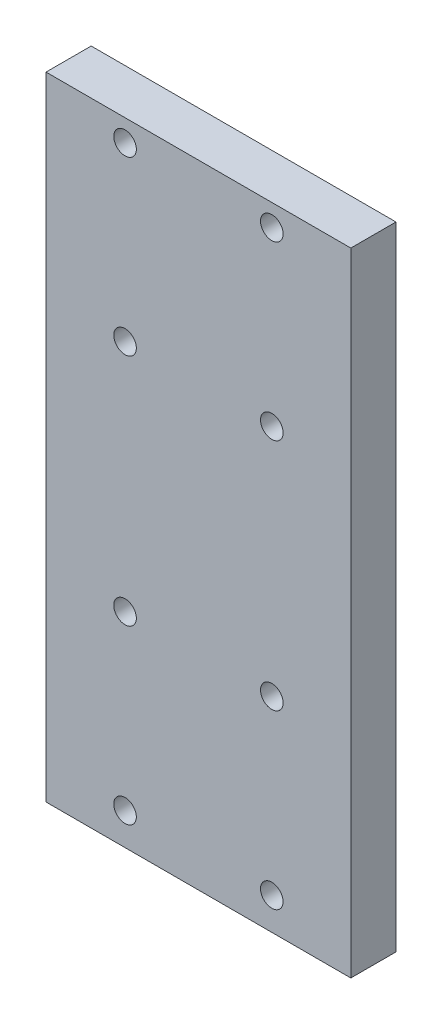
SolidWorks part; units mm, degrees
ref_plane "Front Plane" through (0, 0, 0) normal (0, 0, 1) x (1, 0, 0)
ref_plane "Top Plane" through (0, 0, 0) normal (0, 1, 0) x (1, 0, 0)
ref_plane "Right Plane" through (0, 0, 0) normal (1, 0, 0) x (0, 0, -1)
sketch "Sketch1" plane through (0, 0, 0) normal (0, 0, 1) x (1, 0, 0)
  line L0 (0, 56) -> (0, -56) construction
  line L1 (-27, -56) -> (27, -56)
  line L2 (-27, -56) -> (-27, 56)
  line L3 (-27, 56) -> (27, 56)
  line L4 (27, -56) -> (27, 56)
  line L5 (-27, -56) -> (27, 56) construction
  line L6 (-27, 56) -> (27, -56) construction
  line L7 (-27, -35.05) -> (0, -35.05) construction
  line L8 (-27, 36.89) -> (0, 36.89) construction
  line L10 (-13, 21.64) -> (13, 21.64) construction
  line L11 (-13, 21.64) -> (-13, 52.14) construction
  line L12 (-13, 52.14) -> (13, 52.14) construction
  line L13 (13, 21.64) -> (13, 52.14) construction
  line L14 (-13, 21.64) -> (13, 52.14) construction
  line L15 (-13, 52.14) -> (13, 21.64) construction
  line L16 (-13, -50.3) -> (13, -50.3) construction
  line L17 (-13, -50.3) -> (-13, -19.8) construction
  line L18 (-13, -19.8) -> (13, -19.8) construction
  line L19 (13, -50.3) -> (13, -19.8) construction
  line L20 (-13, -50.3) -> (13, -19.8) construction
  line L21 (-13, -19.8) -> (13, -50.3) construction
  circle A0 centre (-13, 52.14) radius 2
  circle A1 centre (13, 52.14) radius 2
  circle A2 centre (13, 21.64) radius 2
  circle A3 centre (-13, 21.64) radius 2
  circle A4 centre (13, -19.8) radius 2
  circle A5 centre (-13, -19.8) radius 2
  circle A6 centre (-13, -50.3) radius 2
  circle A7 centre (13, -50.3) radius 2
  point P0 (0, 0)
  dimension "D1" = 112
  dimension "D2" = 54
  dimension "D3" = 71.94
  dimension "D4" = 5.7
  dimension "D5" = 26
  dimension "D6" = 30.5
  dimension "D7" = 26
  dimension "D8" = 30.5
extrude "Boss-Extrude1" add sketch "Sketch1" along normal blind 8
